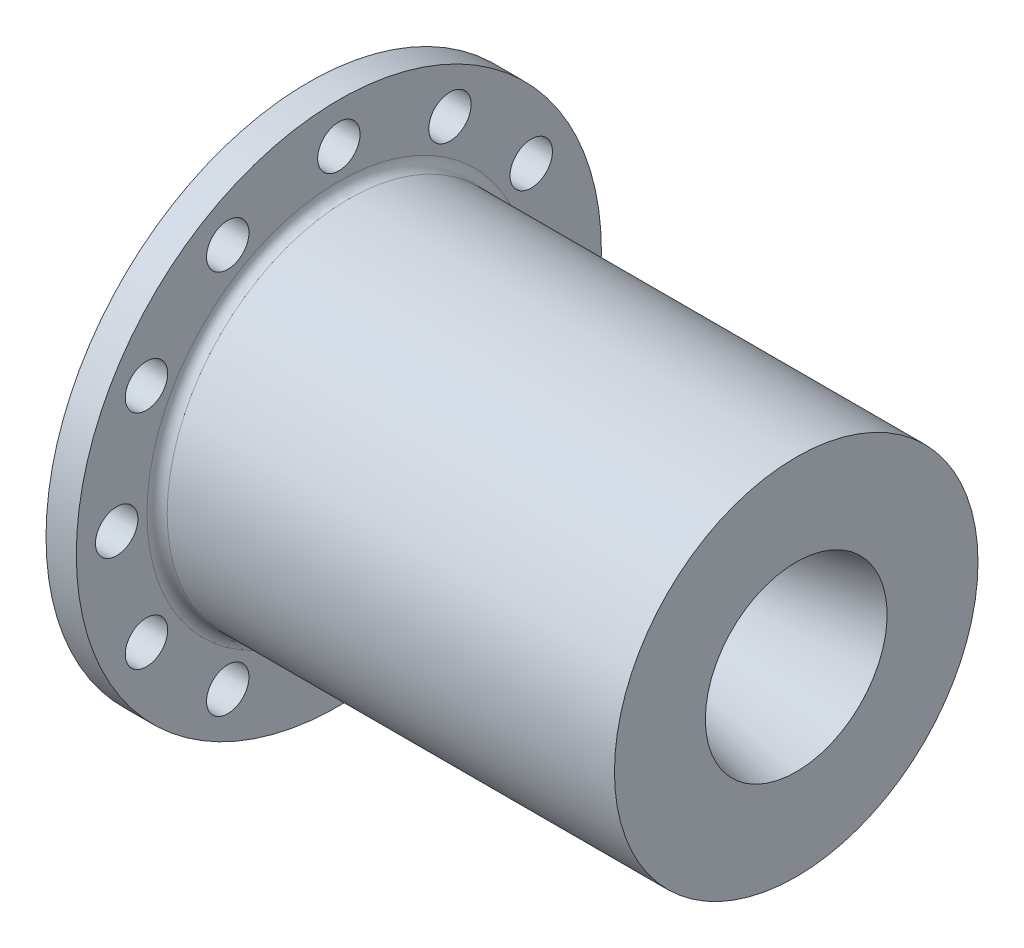
SolidWorks part; units mm, degrees
ref_plane "Front Plane" through (0, 0, 0) normal (0, 0, 1) x (1, 0, 0)
ref_plane "Top Plane" through (0, 0, 0) normal (0, 1, 0) x (1, 0, 0)
ref_plane "Right Plane" through (0, 0, 0) normal (1, 0, 0) x (0, 0, -1)
sketch "Chamber Revolve" plane through (0, 0, 0) normal (0, 0, 1) x (1, 0, 0)
  line L0 (3.81, 22.86) -> (61.3318, 22.86)
  line L1 (61.3318, 22.86) -> (61.3318, 11.43)
  line L2 (61.3318, 11.43) -> (43.198, 7.5756)
  line L3 (43.198, 7.5756) -> (41.674, 7.5756)
  line L4 (41.674, 7.5756) -> (38.1, 15.24)
  line L5 (38.1, 15.24) -> (0, 15.24)
  line L6 (0, 15.24) -> (0, 19.304)
  line L7 (0, 19.304) -> (1.016, 19.304)
  line L8 (1.016, 19.304) -> (1.016, 21.844)
  line L9 (1.016, 21.844) -> (0, 21.844)
  line L10 (0, 21.844) -> (0, 33.02)
  line L11 (0, 33.02) -> (3.81, 33.02)
  line L12 (3.81, 33.02) -> (3.81, 22.86)
  line L13 (0, 0) -> (66.3921, 0) construction
  point P15 (0, 0)
  point P16 (48.7693, 7.5756)
  point P18 (43.9865, 7.5756)
  point P19 (0, 16.7019)
  point P20 (4.361, 29.0526)
  dimension "D1" = 15.1511
  dimension "D2" = 30.48
  dimension "D3" = 22.86
  dimension "D5" = 38.1
  dimension "D6" = 65
  dimension "D8" = 1.524
  dimension "D9" = 4.064
  dimension "D10" = 1.016
  dimension "D11" = 2.54
  dimension "D12" = 10.16
  dimension "D13" = 3.81
revolve "Revolve1" add sketch "Chamber Revolve" angle 360 about L13
fillet "Fillet1" radius 1.27 1 edges at (3.81, 0, 22.86)
sketch "Sketch2" plane through (0, 0, 0) normal (-1, 0, 0) x (0, 0, 1)
  line L0 (0, 0) -> (0, 33.02) construction
  circle A0 centre (0, 27.94) radius 2.667
  circle A1 centre (0, 0) radius 33.02 construction
  point P8 (0, 27.94)
  dimension "D2" = 5.334
  dimension "D1" = 5.08
extrude "Cut-Extrude1" cut sketch "Sketch2" against normal up to next (3.81 mm away)
pattern_circular "CirPattern1" count 12 over 360 about axis through (0, 0, 0) along (1, 0, 0) of "Cut-Extrude1"
fillet "Fillet2" radius 0.254 2 edges at (1.016, 0, 19.304) (1.016, 0, 21.844)
equation "\"Throat Diameter\"= 0.5965"
equation "\"D1@Chamber Revolve\"=\"Throat Diameter\""
equation "\"Exit Diameter\"= 0.90"
equation "\"D3@Chamber Revolve\"=\"Exit Diameter\""
